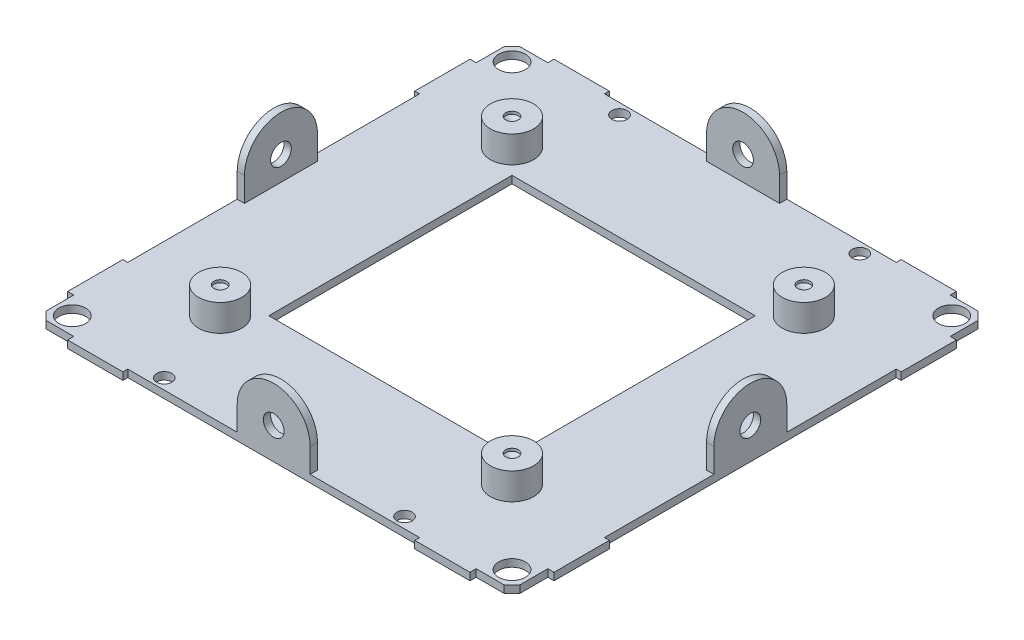
SolidWorks part; units mm, degrees
material "5052-H38"
ref_plane "Front Plane" through (0, 0, 0) normal (0, 0, 1) x (1, 0, 0)
ref_plane "Top Plane" through (0, 0, 0) normal (0, 1, 0) x (1, 0, 0)
ref_plane "Right Plane" through (0, 0, 0) normal (1, 0, 0) x (0, 0, -1)
sketch "Sketch1" plane through (0, 0, 0) normal (0, 1, 0) x (1, 0, 0)
  line L0 (-50, 50) -> (-41.364, 50)
  line L1 (-50, -50) -> (50, -50)
  line L2 (-50, -50) -> (-50, 50)
  line L3 (-50, 50) -> (50, 50)
  line L4 (50, -50) -> (50, 50)
  line L5 (-50, -50) -> (50, 50) construction
  line L6 (-50, 50) -> (50, -50) construction
  line L7 (-50, 50) -> (-50, 41.364)
  line L8 (-50, 41.364) -> (-48.73, 41.364)
  line L9 (-48.73, 41.364) -> (-48.73, 47.079)
  line L10 (-41.364, 50) -> (-41.364, 48.73)
  line L11 (-41.364, 48.73) -> (-47.079, 48.73)
  line L12 (-47.079, 48.73) -> (-48.73, 47.079)
  line L13 (-50, 50) -> (-45.2, 50) construction
  line L14 (-45.2, 50) -> (-45.2, 45.2) construction
  line L15 (50, 50) -> (50, 41.364)
  line L16 (50, 41.364) -> (48.73, 41.364)
  line L17 (48.73, 41.364) -> (48.73, 47.079)
  line L18 (48.73, 47.079) -> (47.079, 48.73)
  line L19 (41.364, 48.73) -> (47.079, 48.73)
  line L20 (41.364, 50) -> (41.364, 48.73)
  line L21 (50, 50) -> (41.364, 50)
  line L22 (50, -50) -> (41.364, -50)
  line L23 (41.364, -50) -> (41.364, -48.73)
  line L24 (41.364, -48.73) -> (47.079, -48.73)
  line L25 (47.079, -48.73) -> (48.73, -47.079)
  line L26 (48.73, -41.364) -> (48.73, -47.079)
  line L27 (50, -41.364) -> (48.73, -41.364)
  line L28 (50, -50) -> (50, -41.364)
  line L29 (-50, -50) -> (-50, -41.364)
  line L30 (-50, -41.364) -> (-48.73, -41.364)
  line L31 (-48.73, -41.364) -> (-48.73, -47.079)
  line L32 (-48.73, -47.079) -> (-47.079, -48.73)
  line L33 (-41.364, -48.73) -> (-47.079, -48.73)
  line L34 (-41.364, -50) -> (-41.364, -48.73)
  line L35 (-50, -50) -> (-41.364, -50)
  line L36 (0, -50) -> (0, 50) construction
  line L37 (-1000, 46.8) -> (49000, 46.8) construction
  line L38 (24.7, 46.8) -> (-24.7, 46.8)
  line L39 (-1000, 0) -> (49000, 0) construction
  line L41 (-25, -25) -> (25, -25)
  line L42 (-25, -25) -> (-25, 25)
  line L43 (-25, 25) -> (25, 25)
  line L44 (25, -25) -> (25, 25)
  line L45 (-25, -25) -> (25, 25) construction
  line L46 (-25, 25) -> (25, -25) construction
  circle A0 centre (-45.2, 45.2) radius 2.7503
  circle A1 centre (45.2, 45.2) radius 2.7503
  circle A2 centre (45.2, -45.2) radius 2.7503
  circle A3 centre (-45.2, -45.2) radius 2.7503
  circle A4 centre (-24.7, 46.8) radius 1.575
  circle A5 centre (24.7, 46.8) radius 1.575
  circle A6 centre (24.7, -46.8) radius 1.575
  circle A7 centre (-24.7, -46.8) radius 1.575
  point P0 (0, 0)
  point P15 (0, 46.8)
  point P45 (0, 0)
  point P46 (0, 0)
  point P48 (-24.7, 46.8)
  point P53 (0, 46.8)
  point P61 (25, 25)
  point P63 (0, 0)
  dimension "D4" = 4
  dimension "D1" = 100
  dimension "D2" = 100
  dimension "D3" = 8.636
  dimension "D5" = 3.2
  dimension "D6" = 24.7
extrude "Boss-Extrude1" add sketch "Sketch1" along normal blind 1.524 contours L37 A5 L38 A4 A0 L9 L8 L2 L30 L31 L32 L33 L34 L1 L23 L24 L25 L26 L27 L4 L16 L17 A1 A2 A3 A6 A7
sketch "Sketch2" plane through (0, 1.524, 0) normal (0, 1, 0) x (1, 0, 0)
  line L0 (0, -1000) -> (0, 49000) construction
  line L1 (0, 50) -> (0, 45) construction
  line L2 (-41.364, 50) -> (41.364, 50) construction
  line L3 (-7.5, 47.5) -> (7.5, 47.5) construction
  line L4 (-7.5, 47.5) -> (7.5, 47.5)
  line L5 (-7.5, 47.5) -> (-7.5, 50)
  line L6 (7.5, 47.5) -> (7.5, 50)
  line L7 (-7.5, 50) -> (7.5, 50)
  line L8 (47.5, 7.5) -> (47.5, -7.5)
  line L9 (47.5, 7.5) -> (50, 7.5)
  line L10 (50, 7.5) -> (50, -7.5)
  line L11 (47.5, -7.5) -> (50, -7.5)
  line L12 (7.5, -47.5) -> (-7.5, -47.5)
  line L13 (7.5, -47.5) -> (7.5, -50)
  line L14 (7.5, -50) -> (-7.5, -50)
  line L15 (-7.5, -47.5) -> (-7.5, -50)
  line L16 (-47.5, -7.5) -> (-47.5, 7.5)
  line L17 (-47.5, -7.5) -> (-50, -7.5)
  line L18 (-50, -7.5) -> (-50, 7.5)
  line L19 (-47.5, 7.5) -> (-50, 7.5)
  point P10 (0, 47.5)
  point P27 (0, 0)
  dimension "D1" = 15
  dimension "D2" = 4
extrude "Boss-Extrude2" add sketch "Sketch2" along normal blind 12.476 contours L4 L5 L7 L6 | L8 L11 L10 L9 | L12 L15 L14 L13 | L16 L19 L18 L17
sketch "Sketch3" plane through (0, 0, 50) normal (0, 0, 1) x (1, 0, 0)
  line L0 (-1007.5, 1.524) -> (48992.5, 1.524) construction
  line L1 (7.5, 1.524) -> (-7.5, 1.524) construction
  line L2 (-7.5, 14) -> (-7.5, 1.524) construction
  line L3 (0, 1.524) -> (0, 6.5) construction
  line L4 (7.5, 14) -> (7.5, 1.524) construction
  line L5 (7.5, 6.5) -> (7.5, 14)
  line L6 (7.5, 14) -> (-7.5, 14)
  line L7 (-7.5, 14) -> (-7.5, 6.5)
  circle A0 centre (0, 6.5) radius 2.125
  arc A1 (-7.5, 6.5) -> (7.5, 6.5) centre (0, 6.5) cw
  line M4 (7.5, 1.524) -> (7.5, 14)
  line M5 (7.5, 14) -> (-7.5, 14)
  line M6 (-7.5, 14) -> (-7.5, 1.524)
extrude "Cut-Extrude1" cut sketch "Sketch3" against normal through all both and the other way through all contours A1 M5 M4 | A1 L6 M6 | A0
sketch "Sketch4" plane through (-50, 0, 0) normal (-1, 0, 0) x (0, 0, 1)
  line L0 (-992.5, 1.524) -> (49007.5, 1.524) construction
  line L1 (-7.5, 1.524) -> (7.5, 1.524) construction
  line L2 (41.364, 1.524) -> (7.5, 1.524) construction
  line L3 (0, 1.524) -> (0, 6.5) construction
  line L4 (7.5, 14) -> (7.5, 1.524) construction
  line L5 (-7.5, 14) -> (-7.5, 1.524) construction
  line L6 (7.5, 6.5) -> (7.5, 14)
  line L7 (7.5, 14) -> (-7.5, 14)
  line L8 (-7.5, 14) -> (-7.5, 6.5)
  circle A0 centre (0, 6.5) radius 2.125
  arc A1 (7.5, 6.5) -> (-7.5, 6.5) centre (0, 6.5) ccw
  line M4 (7.5, 1.524) -> (7.5, 14)
  line M5 (7.5, 14) -> (-7.5, 14)
  line M6 (-7.5, 14) -> (-7.5, 1.524)
extrude "Cut-Extrude2" cut sketch "Sketch4" against normal through all both and the other way through all contours A0 | A1 M4 M5 | A1 L7 M6
sketch "Sketch5" plane through (0, 0, 0) normal (0, -1, 0) x (1, 0, 0)
  line L0 (-1000, -50) -> (49000, -50) construction
  line L1 (-7.5, -50) -> (7.5, -50) construction
  line L2 (0, -1000) -> (0, 49000) construction
  line L3 (-30, -50) -> (30, -50) construction
  line L4 (-30, -50) -> (-30, -49) construction
  line L5 (-50, 30) -> (-49, 30) construction
  line L6 (-30, -49) -> (30, -49)
  line L7 (-30, -49) -> (-30, -50)
  line L8 (-30, -50) -> (30, -50)
  line L9 (30, -49) -> (30, -50)
  line L10 (-49, 30) -> (-50, 30)
  line L11 (-49, 30) -> (-49, -30)
  line L12 (-49, -30) -> (-50, -30)
  line L13 (-50, 30) -> (-50, -30)
  line L14 (30, 50) -> (30, 49) construction
  line L15 (30, 49) -> (30, 50)
  line L16 (30, 49) -> (-30, 49)
  line L17 (-30, 49) -> (-30, 50)
  line L18 (30, 50) -> (-30, 50)
  line L19 (50, -30) -> (49, -30) construction
  line L20 (49, -30) -> (50, -30)
  line L21 (49, -30) -> (49, 30)
  line L22 (49, 30) -> (50, 30)
  line L23 (50, -30) -> (50, 30)
  point P5 (0, -50)
  point P11 (0, -50)
  point P28 (0, 0)
  dimension "D1" = 4
extrude "Cut-Extrude3" cut sketch "Sketch5" against normal through all both and the other way through all
sketch "Sketch6" plane through (0, 1.524, 0) normal (0, 1, 0) x (1, 0, 0)
  circle A0 centre (30, 30) radius 4.445
  circle A1 centre (30, -30) radius 4.445
  circle A2 centre (-30, -30) radius 4.445
  circle A3 centre (-30, 30) radius 4.445
  point P0 (30, 30)
  point P12 (0, 0)
  dimension "D1" = 4
extrude "Boss-Extrude3" add sketch "Sketch6" along normal blind 5.5
hole_wizard "#5-40 Tapped Hole1" positions "Sketch7" profile "Sketch8" tap size "#5-40" standard "ANSI Inch"
sketch "Sketch7" plane through (0, 7.024, 0) normal (0, 1, 0) x (1, 0, 0)
  point P0 (-17.223, 16.8349)
  point P2 (-17.223, 16.8349)
  point P5 (-30, 30)
  point P8 (-30, -30)
  point P11 (30, -30)
  point P14 (30, 30)
sketch "Sketch8" plane through (-17.223, 7.024, -16.8349) normal (1, 0, 0) x (0, 0, 1)
  line L0 (0, 0) -> (0, 1.3245)
  line L1 (0, 1.3245) -> (1.289, 0.55)
  line L2 (1.289, 0.55) -> (1.289, 0)
  line L5 (1.289, 0) -> (0, 0)
  line L10 (0, 1.3245) -> (-1.289, 0.55) construction
  line L11 (0, -6.35) -> (0, 107.95) construction
  dimension "Tap Drill Dia." = 2.5781
  dimension "Tap Drill Depth" = 0.55
  dimension "Drill Angle" = 118
cosmetic thread "Hole Thread1" parameters "D1"=0.55, "D2"=3.175
cosmetic thread "Hole Thread2" parameters "D1"=0.55, "D2"=3.175
cosmetic thread "Hole Thread3" parameters "D1"=0.55, "D2"=3.175
cosmetic thread "Hole Thread4" parameters "D1"=0.55, "D2"=3.175
